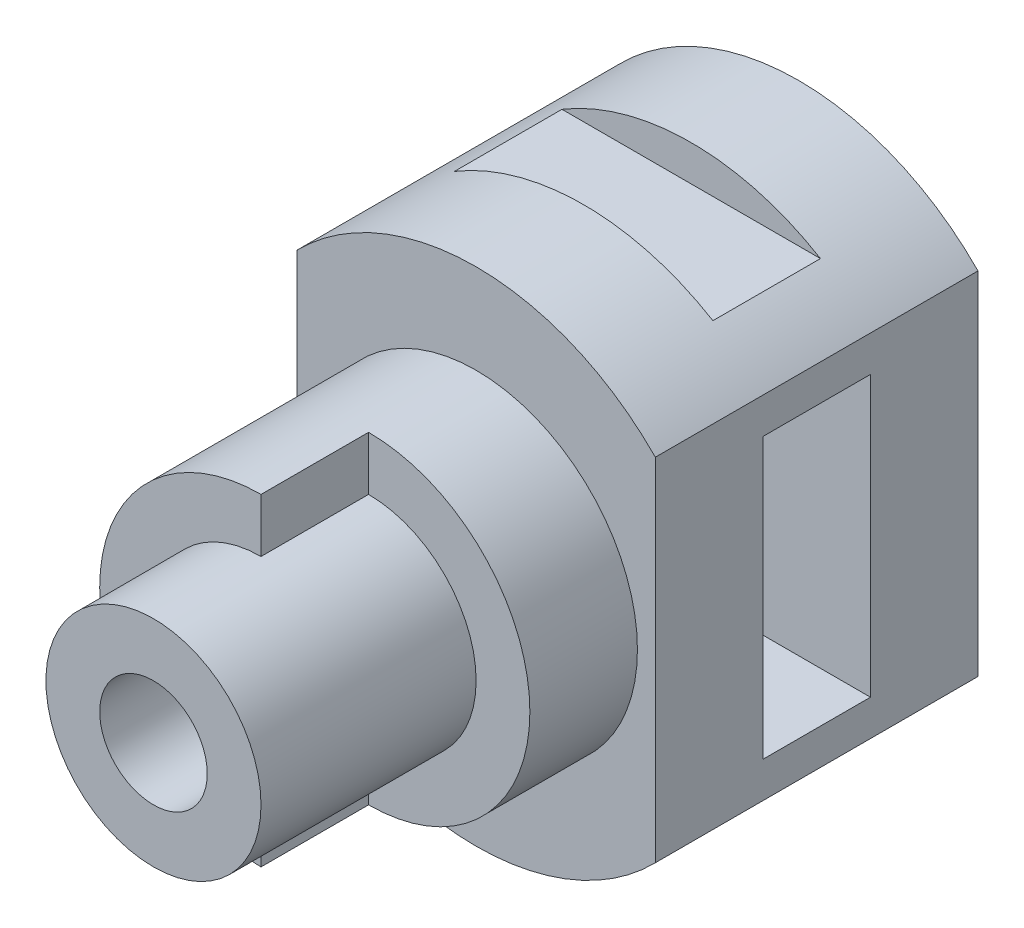
SolidWorks part; units mm, degrees
ref_plane "Front" through (0, 0, 0) normal (0, 0, 1) x (1, 0, 0)
ref_plane "Top" through (0, 0, 0) normal (0, 1, 0) x (1, 0, 0)
ref_plane "Right" through (0, 0, 0) normal (1, 0, 0) x (0, 0, -1)
sketch "Sketch1" plane through (0, 0, 0) normal (0, 0, 1) x (1, 0, 0)
  line L0 (5, -4.899) -> (5, 4.899)
  line L1 (-5, 4.899) -> (-5, -4.899)
  circle A0 centre (0, 0) radius 7
  dimension "D1" = 14
  dimension "D2" = 5
  dimension "D3" = 5
extrude "Boss-Extrude1" add sketch "Sketch1" along normal blind 9 contours L0 A0 L1
sketch "Sketch2" plane through (-5, 0, 0) normal (-1, 0, 0) x (0, 0, 1)
  line L0 (9, -4.899) -> (0, -4.899) construction
  line L3 (3.3522, -7) -> (6, -7)
  line L5 (0, -7) -> (9, -7) construction
  line L6 (9, 7) -> (0, 7) construction
  line L7 (3, 3.899) -> (6, 3.899)
  line L8 (3, 3.899) -> (3, -3.899)
  line L9 (3, -3.899) -> (6, -3.899)
  line L10 (6, 3.899) -> (6, -3.899)
  line L11 (3, 7) -> (6, 7)
  line L12 (3, 7) -> (3, 6)
  line L13 (3, 6) -> (6, 6)
  line L14 (6, 7) -> (6, 6)
  line L15 (0, 7) -> (0, 4.899) construction
  line L16 (0, 4.899) -> (0, -4.899) construction
  line L17 (9, 4.899) -> (0, 4.899) construction
  line L18 (0, -4.899) -> (0, -7) construction
  line L19 (3, -7) -> (6, -7)
  line L20 (3, -7) -> (3, -6)
  line L21 (3, -6) -> (6, -6)
  line L22 (6, -7) -> (6, -6)
  dimension "D1" = 3
  dimension "D2" = 3
  dimension "D3" = 1
  dimension "D4" = 3
  dimension "D5" = 3
  dimension "D6" = 1
  dimension "D7" = 1
  dimension "D8" = 1
  dimension "D9" = 3
  dimension "D10" = 3
extrude "Cut-Extrude1" cut sketch "Sketch2" against normal blind 19 contours L14 L11 L12 L13 | L10 L7 L8 L9 | L3 L22 L21 L20 L19
sketch "Sketch3" plane through (0, 0, 9) normal (0, 0, 1) x (1, 0, 0)
  circle A0 centre (0, 0) radius 4.5
  dimension "D1" = 9
extrude "Boss-Extrude2" add sketch "Sketch3" along normal blind 6
sketch "Sketch4" plane through (0, 0, 15) normal (0, 0, 1) x (1, 0, 0)
  circle A0 centre (0, 0) radius 3
  dimension "D1" = 6
extrude "Boss-Extrude3" add sketch "Sketch4" along normal blind 3
sketch "Sketch7" plane through (0, 0, 18) normal (0, 0, 1) x (1, 0, 0)
  point P0 (0, 0)
hole_wizard "Ø3.0mm Dowel Hole1" positions "3DSketch2" profile "Sketch8" hole size "Ø3.0" standard "ISO"
sketch3d "3DSketch2"
  point P0 (0, 0, 18)
sketch "Sketch8" plane through (0, 0, 18) normal (1, 0, 0) x (0, -1, 0)
  line L0 (0, 0) -> (0, 4.9013)
  line L1 (0, 4.9013) -> (1.5, 4)
  line L2 (1.5, 4) -> (1.5, 0)
  line L5 (1.5, 0) -> (0, 0)
  line L10 (0, 4.9013) -> (-1.5, 4) construction
  line L11 (0, -6.35) -> (0, 107.95) construction
  dimension "Hole Dia." = 3
  dimension "Hole Depth" = 4
  dimension "Drill Angle" = 118
sketch "Sketch9" plane through (0, 0, 15) normal (0, 0, 1) x (1, 0, 0)
  line L0 (0, 4.5) -> (0, 3)
  line L1 (0, -3) -> (0, -4.5)
  arc A0 (0, 3) -> (0, -3) centre (0, 0) cw
  circle A1 centre (0, 0) radius 3 construction
  circle A2 centre (0, 0) radius 3 construction
  arc A3 (0, 4.5) -> (0, -4.5) centre (0, 0) cw
  circle A4 centre (0, 0) radius 4.5 construction
  circle A5 centre (0, 0) radius 4.5 construction
extrude "Cut-Extrude2" cut sketch "Sketch9" against normal blind 3
